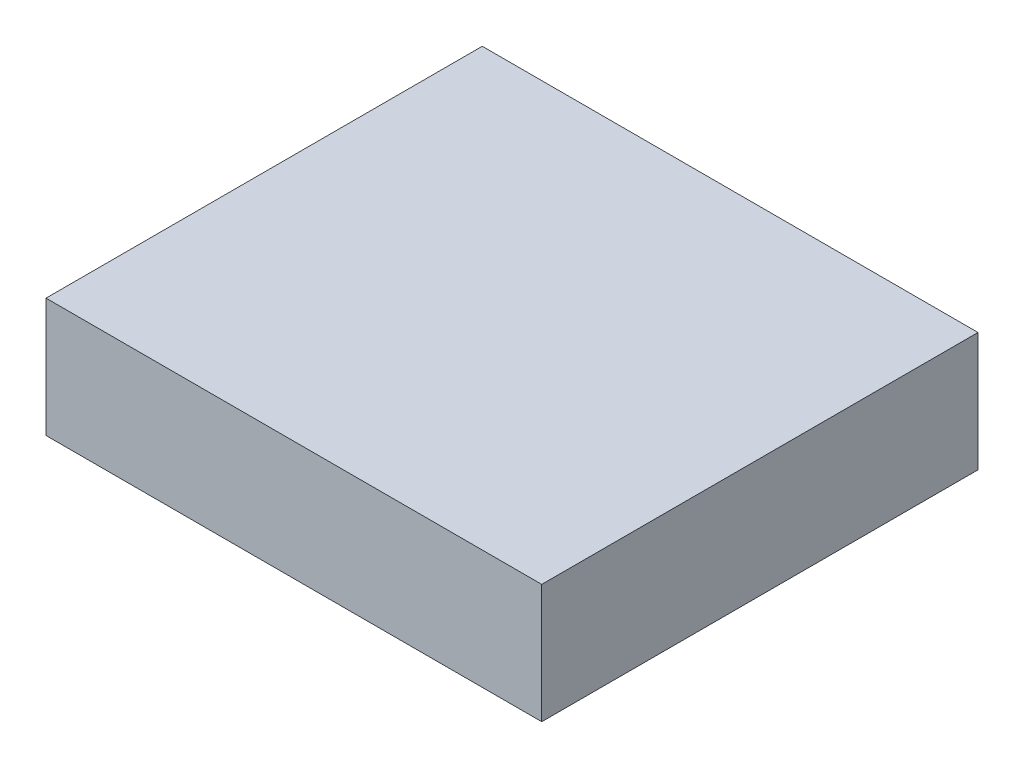
SolidWorks part; units mm, degrees
material "ABS"
ref_plane "Front Plane" through (0, 0, 0) normal (0, 0, 1) x (1, 0, 0)
ref_plane "Top Plane" through (0, 0, 0) normal (0, 1, 0) x (1, 0, 0)
ref_plane "Right Plane" through (0, 0, 0) normal (1, 0, 0) x (0, 0, -1)
sketch "Sketch1" plane through (0, 0, 0) normal (0, 1, 0) x (1, 0, 0)
  line L0 (-2.5, 2.2) -> (2.5, -2.2) construction
  line L1 (-2.5, 2.2) -> (2.5, 2.2)
  line L2 (-2.5, 2.2) -> (-2.5, -2.2)
  line L3 (-2.5, -2.2) -> (2.5, -2.2)
  line L4 (2.5, 2.2) -> (2.5, -2.2)
  point P4 (0, 0)
  dimension "D1" = 5
  dimension "D2" = 4.4
extrude "Boss-Extrude1" add sketch "Sketch1" along normal blind 1.2
sketch "Sketch2" plane through (0, 1.2, 0) normal (0, 1, 0) x (1, 0, 0)
  circle A0 centre (0, 0) radius 0.5
  dimension "D1" = 1
